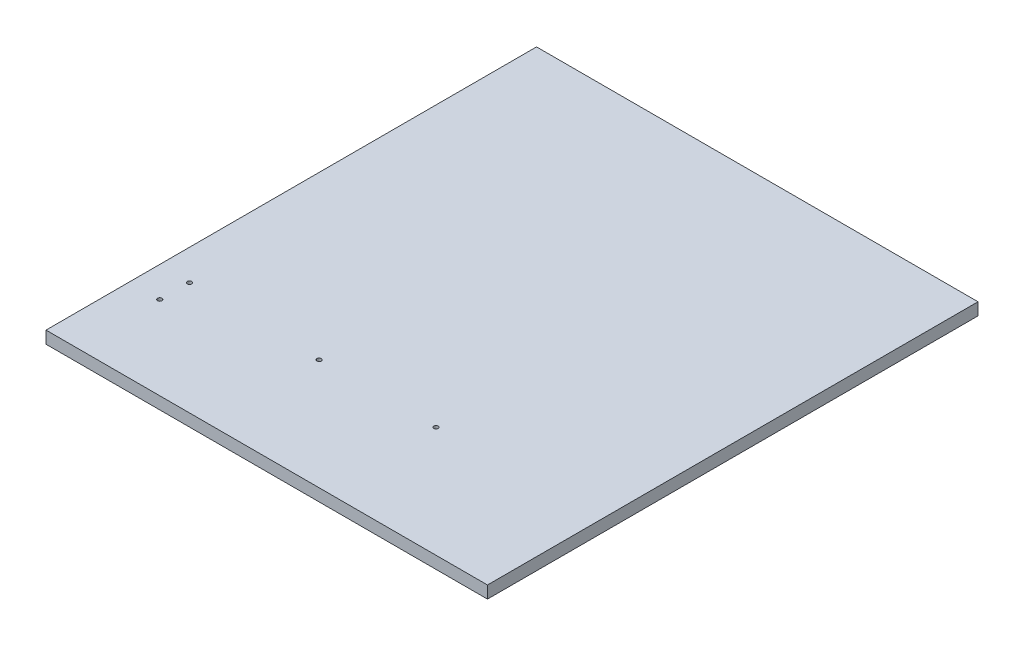
SolidWorks part; units mm, degrees
ref_plane "Front Plane" through (0, 0, 0) normal (0, 0, 1) x (1, 0, 0)
ref_plane "Top Plane" through (0, 0, 0) normal (0, 1, 0) x (1, 0, 0)
ref_plane "Right Plane" through (0, 0, 0) normal (1, 0, 0) x (0, 0, -1)
sketch "Sketch1" plane through (0, 0, 0) normal (0, 1, 0) x (1, 0, 0)
  line L1 (0, 0) -> (228.6, 0)
  line L2 (0, 0) -> (0, 254)
  line L3 (0, 254) -> (228.6, 254)
  line L4 (228.6, 0) -> (228.6, 254)
  dimension "D1" = 228.6
  dimension "D2" = 254
extrude "Boss-Extrude1" add sketch "Sketch1" along normal blind 6.35
hole_wizard "#4-40 Tapped Hole1" positions "Sketch2" profile "Sketch3" tap size "#4-40" standard "ANSI Inch" end condition through all
sketch "Sketch2" plane through (0, 6.35, 0) normal (0, 1, 0) x (1, 0, 0)
  circle A0 centre (84.0588, 57.3884) radius 1.4224
  circle A1 centre (144.5617, 57.3884) radius 1.4224
  point P0 (15.7352, 43.18)
  point P3 (15.875, 58.42)
  point P7 (84.0588, 57.3884)
  point P10 (144.5617, 57.3884)
  point P22 (144.5617, 57.3884)
  dimension "D2" = 2.8448
  dimension "D1" = 2.8448
sketch "Sketch3" plane through (15.7352, 6.35, -43.18) normal (1, 0, 0) x (0, 0, 1)
  line L0 (0, 0) -> (0, 6.35)
  line L1 (0, 6.35) -> (1.1303, 6.35)
  line L2 (1.1303, 6.35) -> (1.1303, 0)
  line L5 (1.1303, 0) -> (0, 0)
  line L11 (0, -6.35) -> (0, 107.95) construction
  dimension "Thru Tap Drill Dia." = 2.2606
  dimension "Thru Tap Drill Depth" = 6.35
cosmetic thread "Hole Thread1"
cosmetic thread "Hole Thread2"
cosmetic thread "Hole Thread3"
cosmetic thread "Hole Thread4"
